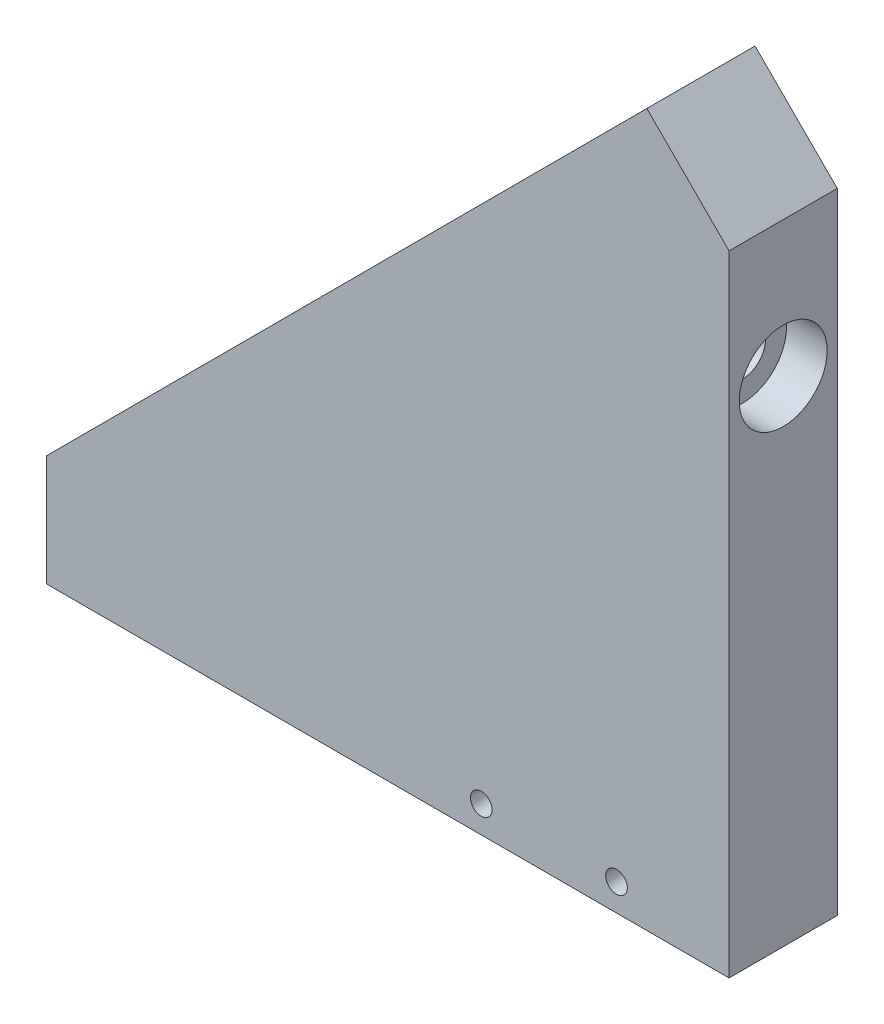
SolidWorks part; units mm, degrees
material "A286 Iron Base Superalloy"
ref_plane "Front Plane" through (0, 0, 0) normal (0, 0, 1) x (1, 0, 0)
ref_plane "Top Plane" through (0, 0, 0) normal (0, 1, 0) x (1, 0, 0)
ref_plane "Right Plane" through (0, 0, 0) normal (1, 0, 0) x (0, 0, -1)
sketch "Sketch2" plane through (0, 0, 0) normal (0, 0, 1) x (1, 0, 0)
  line L0 (-8.3606, 17.4092) -> (51.3194, 17.4092)
  line L1 (51.3194, 17.4092) -> (51.3194, 71.6536)
  line L2 (51.3194, 71.6536) -> (36.0094, 71.6536)
  line L3 (36.0094, 71.6536) -> (43.084, 64.586)
  line L4 (43.084, 64.586) -> (-1.286, 20.1717)
  line L5 (-1.286, 20.1717) -> (-8.3606, 27.2392)
  line L6 (-8.3606, 27.2392) -> (-8.3606, 17.4092)
  dimension "D1" = 10
  dimension "D2" = 10
  dimension "D3" = 15.31
  dimension "D4" = 9.83
  dimension "D5" = 59.68
  dimension "D6" = 62.78
  dimension "D7" = 54.2443
extrude "Boss-Extrude1" add sketch "Sketch2" along normal mid plane 8
sketch "Sketch3" plane through (0, 17.4092, 0) normal (0, -1, 0) x (1, 0, 0)
  line L1 (-8.3606, -4) -> (51.3194, -4)
  line L2 (-8.3606, -4) -> (-8.3606, 4)
  line L3 (-8.3606, 4) -> (51.3194, 4)
  line L4 (51.3194, -4) -> (51.3194, 4)
extrude "Boss-Extrude2" add sketch "Sketch3" along normal blind 5.46
sketch "Sketch5" plane through (0, 0, 4) normal (0, 0, 1) x (1, 0, 0)
  line L0 (51.3194, 11.9492) -> (-8.3606, 11.9492) construction
  line L1 (51.3194, 71.6536) -> (49.1594, 71.6536)
  line L2 (51.3194, 71.6536) -> (51.3194, 11.9492)
  line L3 (51.3194, 11.9492) -> (49.1594, 11.9492)
  line L4 (49.1594, 71.6536) -> (49.1594, 11.9492)
  dimension "D1" = 2.16
extrude "Cut-Extrude2" cut sketch "Sketch5" against normal through all
sketch "Sketch6" plane through (-10.7295, 10.7188, 0) normal (-0.7075, 0.7068, 0) x (0, 0, 1)
  line L0 (4, 13.3618) -> (-4, 13.3618) construction
  line L1 (4, 76.1418) -> (-4, 76.1418) construction
  line L2 (4, 76.1418) -> (4, 13.3618) construction
  circle A0 centre (0, 71.1418) radius 1.5
  circle A1 centre (0, 18.3618) radius 1.5
  dimension "D1" = 3
  dimension "D2" = 3
  dimension "D3" = 5
  dimension "D4" = 5
  dimension "D5" = 4
  dimension "D6" = 4
sketch "Sketch9" plane through (0, 0, 4) normal (0, 0, 1) x (1, 0, 0)
  line L0 (36.0094, 71.6536) -> (49.1594, 58.5036)
  line L1 (49.1594, 71.6536) -> (49.1594, 11.9492) construction
  line L2 (36.0094, 71.6536) -> (49.1594, 71.6536)
  line L6 (49.1594, 58.5036) -> (49.1594, 71.6536)
extrude "Cut-Extrude3" cut sketch "Sketch9" against normal through all
sketch "Sketch10" plane through (0, 11.9492, 0) normal (0, -1, 0) x (1, 0, 0)
  line L0 (-8.3606, 4) -> (-8.3606, -4) construction
  circle A0 centre (10.6394, 0) radius 1.5
  dimension "D1" = 19
hole_wizard "CBORE for M3 SHCS1" positions "Sketch12" profile "Sketch13" counterbore size "M3" standard "ANSI Metric"
sketch "Sketch12" plane through (0, 11.9492, 0) normal (0, -1, 0) x (-1, 0, 0)
  point P0 (-10.6394, 0)
sketch "Sketch13" plane through (10.6394, 11.9492, 0) normal (1, 0, 0) x (0, 0, -1)
  line L0 (0, 0) -> (0, 52.6332)
  line L1 (0, 52.6332) -> (1.7, 52.6332)
  line L3 (1.7, 52.6332) -> (1.7, 3)
  line L4 (1.7, 3) -> (3.25, 3)
  line L5 (3.25, 3) -> (3.25, 0)
  line L7 (3.25, 0) -> (0, 0)
  line L11 (0, -6.35) -> (0, 107.95) construction
  dimension "Thru Hole Dia." = 3.4
  dimension "Thru Hole Depth" = 52.6332
  dimension "C'Bore Dia." = 6.5
  dimension "C'Bore Depth" = 3
sketch "Sketch14" plane through (49.1594, 0, 0) normal (1, 0, 0) x (0, 0, -1)
  line L0 (4, 58.5036) -> (-4, 58.5036) construction
  circle A0 centre (0, 48.5036) radius 1.5
  dimension "D2" = 3
  dimension "D1" = 10
hole_wizard "CBORE for M3 SHCS2" positions "Sketch16" profile "Sketch15" counterbore size "M3" standard "ANSI Metric" end condition through all
sketch "Sketch16" plane through (49.1594, 0, 0) normal (1, 0, 0) x (0, 0, -1)
  point P0 (0, 48.5036)
sketch "Sketch15" plane through (49.1594, 48.5036, 0) normal (0, 1, 0) x (0, 0, -1)
  line L0 (0, 0) -> (0, 57.52)
  line L1 (0, 57.52) -> (1.7, 57.52)
  line L3 (1.7, 57.52) -> (1.7, 3)
  line L4 (1.7, 3) -> (3.25, 3)
  line L5 (3.25, 3) -> (3.25, 0)
  line L7 (3.25, 0) -> (0, 0)
  line L11 (0, -6.35) -> (0, 107.95) construction
  dimension "Thru Hole Dia." = 3.4
  dimension "Thru Hole Depth" = 57.52
  dimension "C'Bore Dia." = 6.5
  dimension "C'Bore Depth" = 3
sketch "Sketch17" plane through (0, 0, 4) normal (0, 0, 1) x (1, 0, 0)
  line L0 (49.1594, 58.5036) -> (49.1594, 11.9492) construction
  line L1 (49.1594, 11.9492) -> (-8.3606, 11.9492) construction
  circle A0 centre (40.8394, 13.9492) radius 1.5
  circle A1 centre (30.8394, 13.9492) radius 1.5
  dimension "D1" = 3
  dimension "D2" = 3
  dimension "D3" = 8.32
  dimension "D4" = 10
  dimension "D5" = 2
  dimension "D6" = 2
hole_wizard "M2x0.4 Tapped Hole1" positions "Sketch19" profile "Sketch18" tap size "M2x0.4" standard "ANSI Metric"
sketch "Sketch19" plane through (0, 0, 4) normal (0, 0, 1) x (1, 0, 0)
  point P0 (30.8394, 13.9492)
  point P3 (40.8394, 13.9492)
sketch "Sketch18" plane through (30.8394, 13.9492, 4) normal (1, 0, 0) x (0, -1, 0)
  line L0 (0, 0) -> (0, 7.4807)
  line L1 (0, 7.4807) -> (0.8, 7)
  line L2 (0.8, 7) -> (0.8, 0)
  line L5 (0.8, 0) -> (0, 0)
  line L10 (0, 7.4807) -> (-0.8, 7) construction
  line L11 (0, -6.35) -> (0, 107.95) construction
  dimension "Tap Drill Dia." = 1.6
  dimension "Tap Drill Depth" = 7
  dimension "Drill Angle" = 118
cosmetic thread "Hole Thread1" parameters "D1"=4, "D2"=2
cosmetic thread "Hole Thread2" parameters "D1"=4, "D2"=2
sketch "Sketch20" plane through (0, 0, 4) normal (0, 0, 1) x (1, 0, 0)
  line L0 (-1.286, 20.1717) -> (-1.286, 11.9492)
  line L1 (49.1594, 11.9492) -> (-8.3606, 11.9492) construction
  line L2 (-1.286, 11.9492) -> (-8.3606, 11.9492)
  line L3 (-8.3606, 11.9492) -> (-8.3606, 27.2392)
  line L4 (-8.3606, 27.2392) -> (-1.286, 20.1717)
extrude "Cut-Extrude4" cut sketch "Sketch20" against normal through all
sketch "Sketch21" plane through (-1.286, 0, 0) normal (-1, 0, 0) x (0, 0, 1)
  line L0 (-4, 11.9492) -> (4, 11.9492) construction
  circle A0 centre (0, 15.9492) radius 1.5
  dimension "D1" = 3
  dimension "D2" = 4
sketch "Sketch22" plane through (-10.7295, 10.7188, 0) normal (-0.7075, 0.7068, 0) x (0, 0, 1)
  line L0 (4, 13.3618) -> (-4, 13.3618) construction
  line L1 (-4, 76.1368) -> (-4, 13.3618) construction
  circle A0 centre (0, 23.3618) radius 1.5
  dimension "D1" = 3
  dimension "D2" = 10
  dimension "D3" = 4
extrude "Cut-Extrude6" cut sketch "Sketch22" against normal blind 5.5
hole_wizard "M3x0.5 Tapped Hole2" positions "Sketch24" profile "Sketch23" tap size "M3x0.5" standard "ANSI Metric"
sketch "Sketch24" plane through (-1.286, 0, 0) normal (-1, 0, 0) x (0, 0, 1)
  point P0 (0, 15.9492)
sketch "Sketch23" plane through (-1.286, 15.9492, 0) normal (0, 1, 0) x (0, 0, 1)
  line L0 (0, 0) -> (0, 9.2511)
  line L1 (0, 9.2511) -> (1.25, 8.5)
  line L2 (1.25, 8.5) -> (1.25, 0)
  line L5 (1.25, 0) -> (0, 0)
  line L10 (0, 9.2511) -> (-1.25, 8.5) construction
  line L11 (0, -6.35) -> (0, 107.95) construction
  dimension "Tap Drill Dia." = 2.5
  dimension "Tap Drill Depth" = 8.5
  dimension "Drill Angle" = 118
cosmetic thread "Hole Thread3" parameters "D1"=6, "D2"=3
